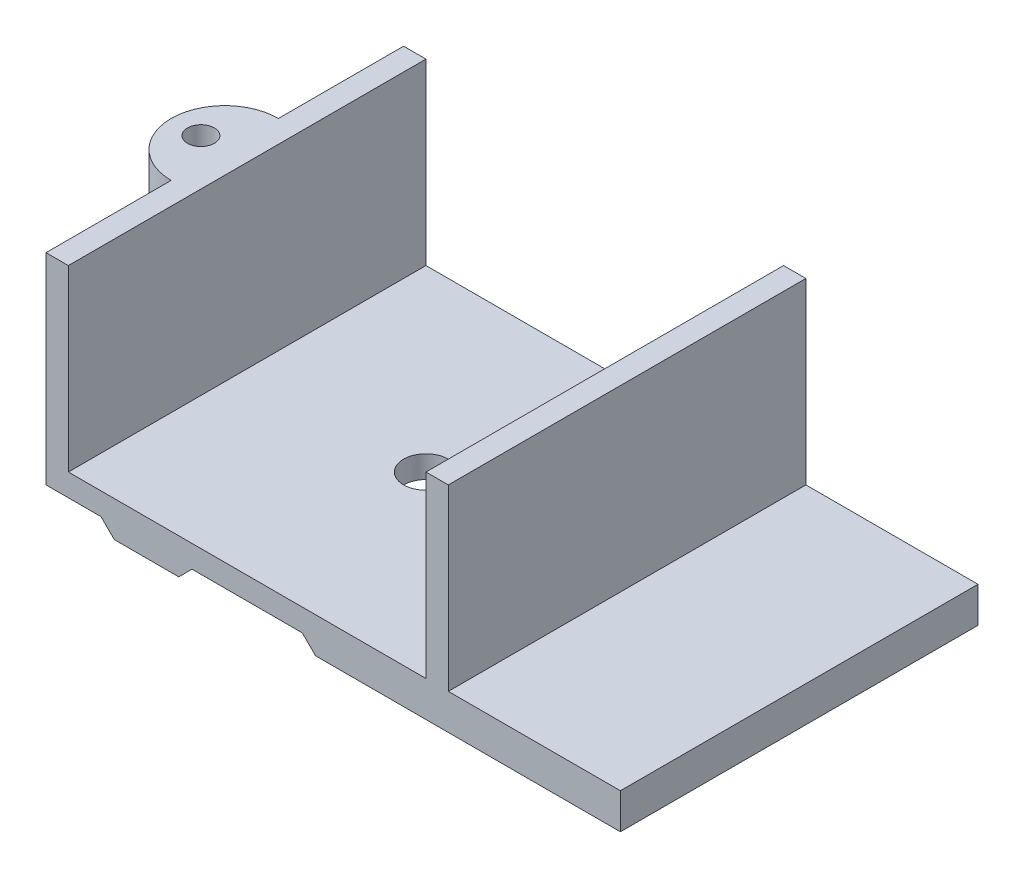
SolidWorks part; units mm, degrees
material "Malleable Cast Iron"
ref_plane "Front Plane" through (0, 0, 0) normal (0, 0, 1) x (1, 0, 0)
ref_plane "Top Plane" through (0, 0, 0) normal (0, 1, 0) x (1, 0, 0)
ref_plane "Right Plane" through (0, 0, 0) normal (1, 0, 0) x (0, 0, -1)
sketch "Sketch1" plane through (0, 0, 0) normal (0, 0, 1) x (1, 0, 0)
  line L1 (0, 0) -> (9.3829, 0)
  line L2 (0, 0) -> (0, 40)
  line L3 (9.3829, 0) -> (25.59, 0)
  line L4 (80, 0) -> (80, 40)
  line L7 (40, 0) -> (40, 16.761) construction
  line L11 (25.59, 0) -> (54.41, 0)
  line L12 (70.6171, 0) -> (80, 0)
  line L13 (80, 40) -> (85, 40)
  line L14 (85, -5) -> (85, 40)
  line L15 (72.6882, -5) -> (85, -5)
  line L16 (72.6882, -5) -> (69.7283, -7.9599)
  line L17 (69.7283, -7.9599) -> (55.2988, -7.9599)
  line L18 (55.2988, -7.9599) -> (52.3389, -5)
  line L19 (27.6611, -5) -> (52.3389, -5)
  line L20 (24.7012, -7.9599) -> (27.6611, -5)
  line L21 (10.2717, -7.9599) -> (24.7012, -7.9599)
  line L22 (7.3118, -5) -> (10.2717, -7.9599)
  line L23 (-5, -5) -> (7.3118, -5)
  line L24 (-5, -5) -> (-5, 40)
  line L25 (0, 40) -> (-5, 40)
  line L26 (-5, -5) -> (-5, 45) construction
  line L27 (54.41, 0) -> (70.6171, 0)
  line L28 (-5, 45) -> (85, 45) construction
  line L29 (85, -5) -> (85, 45) construction
  line L30 (0, 40) -> (80, 40) construction
  line L34 (72.6882, -5) -> (85, -5) construction
  line L35 (12.3428, -2.9599) -> (22.6301, -2.9599) construction
  line L36 (9.3829, 0) -> (12.3428, -2.9599) construction
  line L37 (22.6301, -2.9599) -> (25.59, 0) construction
  line L38 (67.6572, -2.9599) -> (57.3699, -2.9599) construction
  line L39 (57.3699, -2.9599) -> (54.41, 0) construction
  line L40 (70.6171, 0) -> (67.6572, -2.9599) construction
  dimension "D1" = 40
  dimension "D2" = 80
  dimension "D3" = 5
extrude "Boss-Extrude2" add sketch "Sketch1" along normal blind 80
sketch "Sketch2" plane through (0, 40, 0) normal (0, 1, 0) x (1, 0, 0)
  line L0 (-5, -80) -> (-5, 0) construction
  line L1 (-5, -28) -> (-5, -52)
  arc A0 (-5, -28) -> (-5, -52) centre (-5, -40) ccw
  circle A1 centre (-10.3381, -40) radius 3
extrude "Boss-Extrude3" add sketch "Sketch2" against normal up to surface (45 mm away) up to face at (1.1559, -5, 40)
sketch "Sketch3" plane through (0, 0, 0) normal (0, 1, 0) x (1, 0, 0)
  circle A0 centre (40, -40) radius 5
extrude "Cut-Extrude1" cut sketch "Sketch3" against normal through all
ref_plane "Plane1" through (85, 0, 0) normal (1, 0, 0) x (0, 0, -1)
sketch "Sketch5" plane through (85, 0, 0) normal (1, 0, 0) x (0, 0, -1)
  line L0 (-80, -7.9599) -> (0, -7.9599) construction
  line L2 (-80, -5) -> (-80, -7.9599)
  line L3 (-80, -7.9599) -> (0, -7.9599)
  line L4 (0, -5) -> (0, -7.9599)
  line L5 (0, -5) -> (0, 40) construction
  line L7 (-80, -5) -> (-80, 0)
  line L8 (-80, 0) -> (0, 0)
  line L9 (0, -5) -> (0, 0)
  dimension "D1" = 5
extrude "Boss-Extrude4" add sketch "Sketch5" along normal blind 38.5 and the other way up to surface other way up to face at (71.2082, -6.48, 40)
